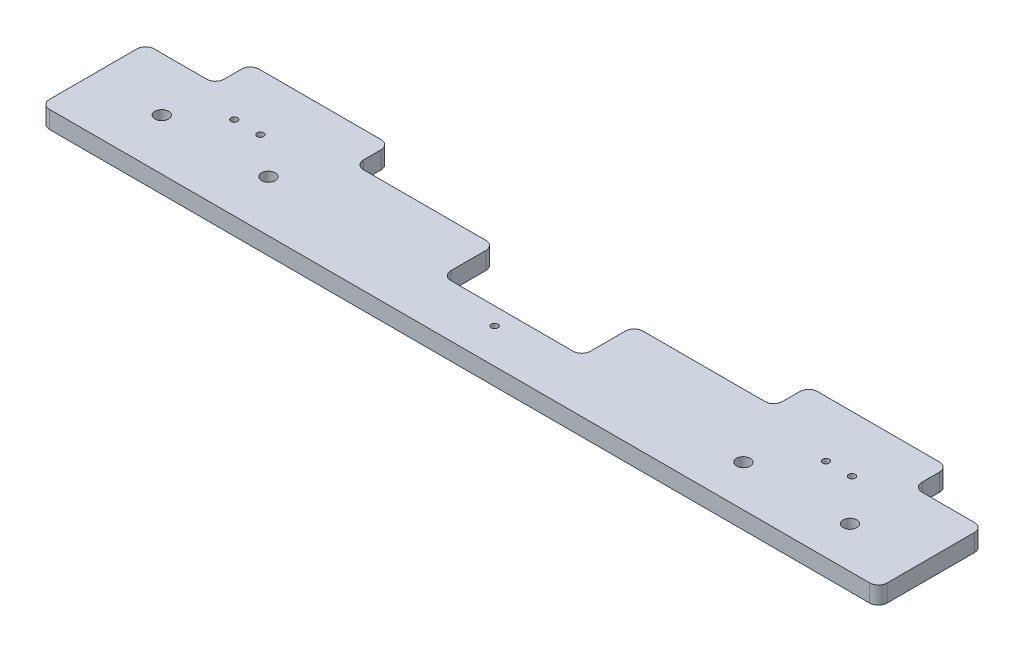
SolidWorks part; units mm, degrees
material "Acrylic (Medium-high impact)"
ref_plane "Front Plane" through (0, 0, 0) normal (0, 0, 1) x (1, 0, 0)
ref_plane "Top Plane" through (0, 0, 0) normal (0, 1, 0) x (1, 0, 0)
ref_plane "Right Plane" through (0, 0, 0) normal (1, 0, 0) x (0, 0, -1)
sketch "Sketch1" plane through (0, 0, 0) normal (0, 1, 0) x (1, 0, 0)
  line L1 (-152.4, -19.05) -> (152.4, -19.05)
  line L2 (-152.4, -19.05) -> (-152.4, 19.05)
  line L3 (-152.4, 19.05) -> (152.4, 19.05)
  line L4 (152.4, -19.05) -> (152.4, 19.05)
  line L5 (-152.4, -19.05) -> (152.4, 19.05) construction
  line L6 (-152.4, 19.05) -> (152.4, -19.05) construction
  point P0 (0, 0)
  dimension "D1" = 304.8
  dimension "D2" = 38.1
extrude "Boss-Extrude1" add sketch "Sketch1" along normal blind 6.35
sketch "Sketch5" plane through (0, 6.35, 0) normal (0, 1, 0) x (1, 0, 0)
  line L0 (-127, 19.05) -> (-127, 31.75)
  line L1 (152.4, 19.05) -> (-152.4, 19.05) construction
  line L2 (-127, 31.75) -> (-76.2, 31.75)
  line L3 (-76.2, 31.75) -> (-76.2, 19.05)
  line L4 (76.2, 19.05) -> (76.2, 31.75)
  line L5 (76.2, 31.75) -> (127, 31.75)
  line L6 (127, 31.75) -> (127, 19.05)
  line L7 (127, 19.05) -> (76.2, 19.05)
  line L8 (-127, 19.05) -> (-76.2, 19.05)
  line L9 (-152.4, 19.05) -> (-152.4, -19.05) construction
  line L10 (152.4, -19.05) -> (152.4, 19.05) construction
  dimension "D1" = 25.4
  dimension "D2" = 50.8
  dimension "D3" = 12.7
  dimension "D4" = 50.8
  dimension "D5" = 12.7
  dimension "D6" = 25.4
extrude "Boss-Extrude2" add sketch "Sketch5" against normal up to surface (6.35 mm away) up to face at (0, 0, 0)
fillet "Fillet1" radius 3.175 8 edges at (127, 3.175, -19.05) (127, 3.175, -31.75) (76.2, 3.175, -31.75) (76.2, 3.175, -19.05) (-76.2, 3.175, -31.75) (-127, 3.175, -31.75)
fillet "Fillet2" radius 3.175 4 edges at (152.4, 3.175, -19.05) (152.4, 3.175, 19.05) (-152.4, 3.175, 19.05) (-152.4, 3.175, -19.05)
sketch "Sketch2" plane through (0, 6.35, 0) normal (0, 1, 0) x (1, 0, 0)
  line L0 (0, 0) -> (0, 12.7) construction
  line L1 (152.4, 19.05) -> (-152.4, 19.05) construction
  circle A0 centre (0, 12.7) radius 1.4732
  dimension "D1" = 2.9464
  dimension "D2" = 6.35
extrude "Cut-Extrude1" cut sketch "Sketch2" against normal up to surface (6.35 mm away) up to face at (3.8365, 0, -16.9333)
sketch "Sketch3" plane through (0, 6.35, 0) normal (0, 1, 0) x (1, 0, 0)
  line L0 (-112.4, 11.35) -> (-102.9, 11.35) construction
  line L1 (-112.4, 11.35) -> (-152.4, 11.35) construction
  line L2 (-152.4, 15.875) -> (-152.4, -15.875) construction
  line L3 (-112.4, 11.35) -> (-112.4, 19.05) construction
  line L4 (152.4, 19.05) -> (-152.4, 19.05) construction
  circle A0 centre (-112.4, 11.35) radius 1.2
  circle A1 centre (-102.9, 11.35) radius 1.2
  dimension "D1" = 2.4
  dimension "D2" = 7.7
  dimension "D3" = 40
  dimension "D4" = 9.5
extrude "Cut-Extrude2" cut sketch "Sketch3" against normal up to surface (6.35 mm away) up to face at (0, 0, -14.1732)
mirror "Mirror1" about plane through (0, 0, 0) normal (1, 0, 0) of "Cut-Extrude2"
sketch "Sketch4" plane through (0, 6.35, 0) normal (0, 1, 0) x (1, 0, 0)
  line L0 (-127, -0.4575) -> (-88.2, -0.4575) construction
  line L1 (88.2, -4.0012) -> (127, -4.0012) construction
  line L2 (-152.4, 15.875) -> (-152.4, -15.875) construction
  line L3 (152.4, -15.875) -> (152.4, 15.875) construction
  circle A0 centre (-127, -0.4575) radius 2.4765
  circle A1 centre (-88.2, -0.4575) radius 2.4765
  circle A2 centre (88.2, -4.0012) radius 2.4765
  circle A3 centre (127, -4.0012) radius 2.4765
  dimension "D1" = 4.953
  dimension "D2" = 38.8
  dimension "D3" = 38.8
  dimension "D4" = 25.4
  dimension "D5" = 25.4
extrude "Cut-Extrude3" cut sketch "Sketch4" against normal up to surface (6.35 mm away) up to face at (102.9, 0, -12.55)
sketch "Sketch6" plane through (0, 6.35, 0) normal (0, 1, 0) x (1, 0, 0)
  line L0 (-25.4, 19.05) -> (-25.4, 0)
  line L1 (73.025, 19.05) -> (-73.025, 19.05) construction
  line L2 (-25.4, 0) -> (25.4, 0)
  line L3 (25.4, 0) -> (25.4, 19.05)
  line L4 (-25.4, 19.05) -> (25.4, 19.05)
  line L5 (0, 0) -> (0, -19.05) construction
  line L6 (-149.225, -19.05) -> (149.225, -19.05) construction
  dimension "D1" = 19.05
  dimension "D2" = 50.8
extrude "Cut-Extrude4" cut sketch "Sketch6" against normal up to surface (6.35 mm away) up to face at (127, 0, 1.5247)
fillet "Fillet3" radius 3.175 4 edges at (25.4, 3.175, -19.05) (25.4, 3.175, 0) (-25.4, 3.175, 0) (-25.4, 3.175, -19.05)
sketch "Sketch7" plane through (0, 6.35, 0) normal (0, 1, 0) x (1, 0, 0)
  line L0 (-22.225, 0) -> (22.225, 0) construction
  line L1 (0, -6.35) -> (0, 0) construction
  line L2 (-22.225, 0) -> (22.225, 0) construction
  circle A0 centre (0, -6.35) radius 1.2192
  dimension "D1" = 2.4384
  dimension "D2" = 6.35
extrude "Cut-Extrude5" cut sketch "Sketch7" against normal up to surface (6.35 mm away) up to face at (1.9844, 0, -15.0813)
equation "\"w\"=12"
equation "\"WIDTH\"=14"
